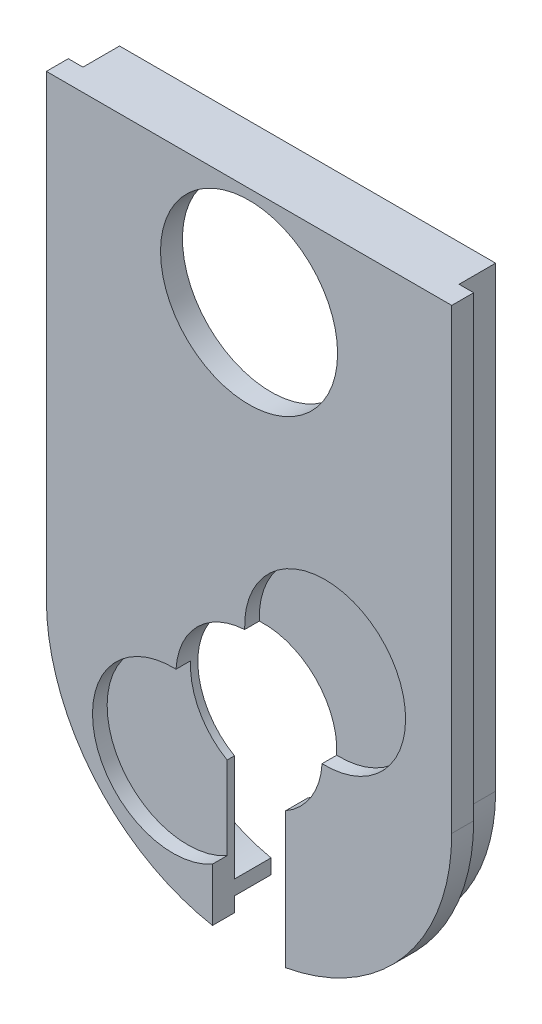
SolidWorks part; units mm, degrees
ref_plane "Front Plane" through (0, 0, 0) normal (0, 0, 1) x (1, 0, 0)
ref_plane "Top Plane" through (0, 0, 0) normal (0, 1, 0) x (1, 0, 0)
ref_plane "Right Plane" through (0, 0, 0) normal (1, 0, 0) x (0, 0, -1)
sketch "Sketch1" plane through (0, 0, 0) normal (0, 0, 1) x (1, 0, 0)
  circle A0 centre (0, 0) radius 30 construction
  circle A2 centre (0, 0) radius 27.7
  dimension "D1" = 2.3
extrude "Boss-Extrude1" add sketch "Sketch1" along normal blind 3
sketch "Sketch2" plane through (0, 0, 3) normal (0, 0, 1) x (1, 0, 0)
  circle A1 centre (-10.3945, -10.3945) radius 11
  circle A2 centre (10.3945, 10.3945) radius 11
  point P1 (0, 0)
  point P3 (-9.7312, -10.3945)
  point P7 (0, 0)
  point P15 (10.3945, 9.7372)
extrude "Cut-Extrude1" cut sketch "Sketch2" against normal blind 2
sketch "Sketch4" plane through (0, 0, 3) normal (0, 0, 1) x (1, 0, 0)
  circle A0 centre (0, 0) radius 10
extrude "Cut-Extrude2" cut sketch "Sketch4" against normal blind 3
sketch "Sketch5" plane through (0, 0, 3) normal (0, 0, 1) x (1, 0, 0)
  line L0 (-27.7, 0) -> (-27.7, 62.5)
  line L1 (-27.7, 62.5) -> (27.7, 62.5)
  line L2 (27.7, 62.5) -> (27.7, 0)
  circle A0 centre (0, 0) radius 27.7 construction
  arc A1 (-27.7, 0) -> (27.7, 0) centre (0, 0) cw
  circle A2 centre (0, 49) radius 12.1
extrude "Boss-Extrude3" add sketch "Sketch5" against normal blind 3 separate body
sketch "Sketch6" plane through (0, 0, 3) normal (0, 0, 1) x (1, 0, 0)
  line L0 (-5, -27.7) -> (5, -27.7)
  line L1 (-5, -27.7) -> (-5, 0)
  line L2 (-5, 0) -> (5, 0)
  line L3 (5, 0) -> (5, -27.7)
  point P3 (0, -27.7)
extrude "Cut-Extrude3" cut sketch "Sketch6" against normal blind 3
sketch "Sketch8" plane through (0, 0, 0) normal (0, 0, -1) x (-1, 0, 0)
  line L1 (-23.7, 62.5) -> (23.7, 62.5)
  line L2 (-27.7, 62.5) -> (27.7, 62.5) construction
  line L3 (-5, -27.245) -> (-5, -8.6603) construction
  line L5 (-25.7, 62.5) -> (-23.7, 62.5)
  line L6 (-25.7, 62.5) -> (-25.7, 0)
  line L8 (-23.7, 61.1) -> (-23.7, 0)
  line L9 (25.7, 62.5) -> (23.7, 62.5)
  line L10 (25.7, 62.5) -> (25.7, 0)
  line L12 (23.7, 61.1) -> (23.7, 0)
  line L13 (-23.7, 61.1) -> (23.7, 61.1)
  line L15 (5, -8.6603) -> (5, -27.245) construction
  line L16 (-5, -25.245) -> (-5, -23.245)
  line L17 (5, -25.245) -> (5, -23.245)
  arc A0 (-25.7, 0) -> (-5, -25.245) centre (0.044, 0) ccw
  arc A1 (-23.7, 0) -> (-5, -23.245) centre (0.0973, 0) ccw
  arc A2 (23.7, 0) -> (5, -23.245) centre (-0.0973, 0) cw
  arc A3 (25.7, 0) -> (5, -25.245) centre (-0.044, 0) cw
  dimension "D1" = 2
extrude "Boss-Extrude4" add sketch "Sketch8" along normal blind 5
